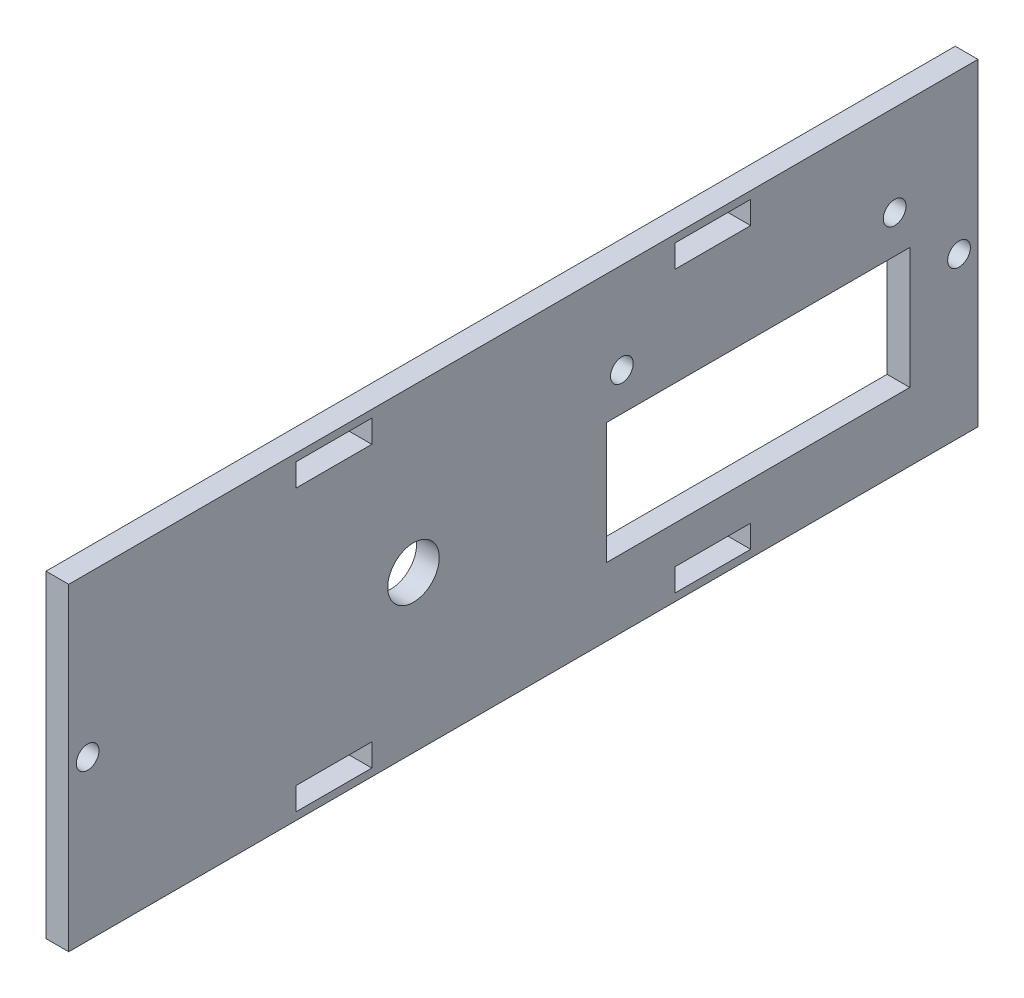
SolidWorks part; units mm, degrees
ref_plane "Front Plane" through (0, 0, 0) normal (0, 0, 1) x (1, 0, 0)
ref_plane "Top Plane" through (0, 0, 0) normal (0, 1, 0) x (1, 0, 0)
ref_plane "Right Plane" through (0, 0, 0) normal (1, 0, 0) x (0, 0, -1)
sketch "Sketch1" plane through (0, 0, 0) normal (1, 0, 0) x (0, 0, -1)
  line L1 (30, -17) -> (20, -17)
  line L2 (-20, -17) -> (-30, -17)
  line L13 (30, 17) -> (20, 17)
  line L14 (30, 20) -> (20, 20)
  line L15 (30, 20) -> (30, 17)
  line L17 (20, 20) -> (20, 17)
  line L18 (30, 20) -> (20, 17) construction
  line L22 (0, 0) -> (0, 41.0344) construction
  line L24 (11, -12) -> (51, -12)
  line L25 (30, 17) -> (20, 20) construction
  line L26 (30, -17) -> (30, -20)
  line L27 (30, -20) -> (20, -20)
  line L28 (20, -17) -> (20, -20)
  line L29 (30, -17) -> (20, -20) construction
  line L30 (30, -20) -> (20, -17) construction
  line L31 (51, -12) -> (51, 4)
  line L32 (-20, 20) -> (-30, 20)
  line L33 (-20, 20) -> (-20, 17)
  line L34 (51, 4) -> (11, 4)
  line L35 (-30, 20) -> (-30, 17)
  line L36 (-20, 20) -> (-30, 17) construction
  line L37 (-20, 17) -> (-30, 20) construction
  line L38 (-20, -17) -> (-20, -20)
  line L39 (-20, -20) -> (-30, -20)
  line L40 (-30, -17) -> (-30, -20)
  line L41 (-20, -17) -> (-30, -20) construction
  line L42 (-20, -20) -> (-30, -17) construction
  line L43 (0, 0) -> (0, -51.197) construction
  line L44 (11, 4) -> (11, -12)
  line L45 (60, -21) -> (-60, -21)
  line L46 (60, -21) -> (60, 21)
  line L47 (60, 21) -> (-60, 21)
  line L48 (11, -12) -> (51, -12)
  line L49 (51, -12) -> (51, 4)
  line L50 (51, 4) -> (11, 4)
  line L51 (11, 4) -> (11, -12)
  line L56 (-60, -21) -> (-60, 21)
  line L57 (60, -21) -> (-60, 21) construction
  line L58 (60, 21) -> (-60, -21) construction
  line L59 (-20, 17) -> (-30, 17)
  circle A1 centre (49, 9) radius 1.5 construction
  circle A4 centre (13, 9) radius 1.5 construction
  circle A5 centre (49, 9) radius 1.5
  circle A6 centre (13, 9) radius 1.5
  circle A7 centre (-14.5, -0.4) radius 3.4 construction
  circle A8 centre (-14.5, -0.4) radius 3.4
  circle A9 centre (57.5, 0) radius 1.5
  circle A10 centre (-57.5, 0) radius 1.5
  point P0 (0, 0)
  point P1 (0, 0)
  point P2 (0, 21)
  point P3 (60, 0)
  point P4 (0, 0)
  point P15 (25, 18.5)
  point P25 (25, -18.5)
  point P32 (-25, 18.5)
  point P37 (-25, -18.5)
  point P50 (60, 5.1843)
  dimension "D19" = 3
  dimension "D3" = 2.5
  dimension "D4" = 2.5
  dimension "D5" = 3
  dimension "D6" = 10
  dimension "D7" = 2.5
  dimension "D8" = 0
  dimension "D9" = 3
  dimension "D10" = 10
  dimension "D11" = 3
  dimension "D12" = 10
  dimension "D13" = 3
  dimension "D14" = 10
  dimension "D15" = 20
  dimension "D16" = 20
  dimension "D17" = 20
  dimension "D18" = 20
  dimension "D20" = 42
  dimension "D21" = 120
  dimension "D22" = 2.5
extrude "Boss-Extrude1" add sketch "Sketch1" along normal blind 3
